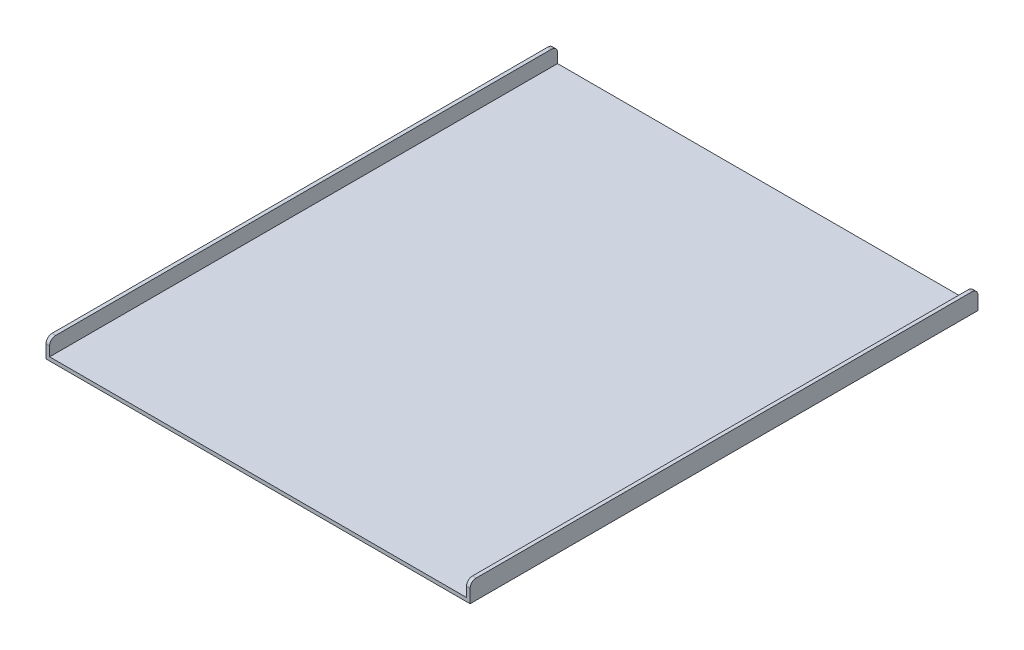
SolidWorks part; units mm, degrees
ref_plane "Front Plane" through (0, 0, 0) normal (0, 0, 1) x (1, 0, 0)
ref_plane "Top Plane" through (0, 0, 0) normal (0, 1, 0) x (1, 0, 0)
ref_plane "Right Plane" through (0, 0, 0) normal (1, 0, 0) x (0, 0, -1)
sketch "Sketch1" plane through (0, 0, 0) normal (0, 0, 1) x (1, 0, 0)
  line L0 (-250.5141, 25.7536) -> (-250.5141, 0)
  line L1 (-250.5141, 0) -> (440.5033, 0)
  line L2 (440.5033, 0) -> (440.5033, 25.9157)
  dimension "D1" = 691.0174
  dimension "D2" = 250.5141
  dimension "D3" = 25.7536
  dimension "D4" = 25.9157
extrude "Extrude-Thin1" add sketch "Sketch1" along normal mid plane 842.0984 thin
sketch "Sketch3" plane through (446.5515, 0, 0) normal (1, 0, 0) x (0, 0, -1)
  line L0 (-300, 23.9518) -> (0, 23.9518) construction
  line L1 (-300, 28.9518) -> (0, 28.9518)
  line L2 (-300, 18.9518) -> (0, 18.9518)
  line L3 (-421.0492, -6.0482) -> (421.0492, -6.0482) construction
  line L4 (421.0492, -6.0482) -> (421.0492, 25.9157) construction
  circle A0 centre (391.0492, 23.9518) radius 5
  arc A1 (-300, 28.9518) -> (-300, 18.9518) centre (-300, 23.9518) ccw
  arc A2 (0, 18.9518) -> (0, 28.9518) centre (0, 23.9518) ccw
  point P4 (-150, 23.9518)
  dimension "D1" = 10
  dimension "D2" = 30
  dimension "D3" = 30
  dimension "D4" = 150
  dimension "D5" = 300
  dimension "D6" = 10
fillet "Fillet1" radius 10 4 edges at (-253.5382, 25.7536, -421.0492) (443.5274, 25.9157, -421.0492) (443.5274, 25.9157, 421.0492) (-253.5382, 25.7536, 421.0492)
sketch "草图2" plane through (0, -6.0482, 0) normal (0, -1, 0) x (-1, 0, 0)
  circle A0 centre (-360.1647, 358.0127) radius 19.05
extrude "凸台-拉伸1" add sketch "草图2" along normal blind 23.2497 contours A0
sketch "草图3" plane through (0, -6.0482, 0) normal (0, -1, 0) x (-1, 0, 0)
  circle A0 centre (175.4103, -359.7212) radius 19.05
extrude "凸台-拉伸2" add sketch "草图3" along normal blind 26 contours A0
